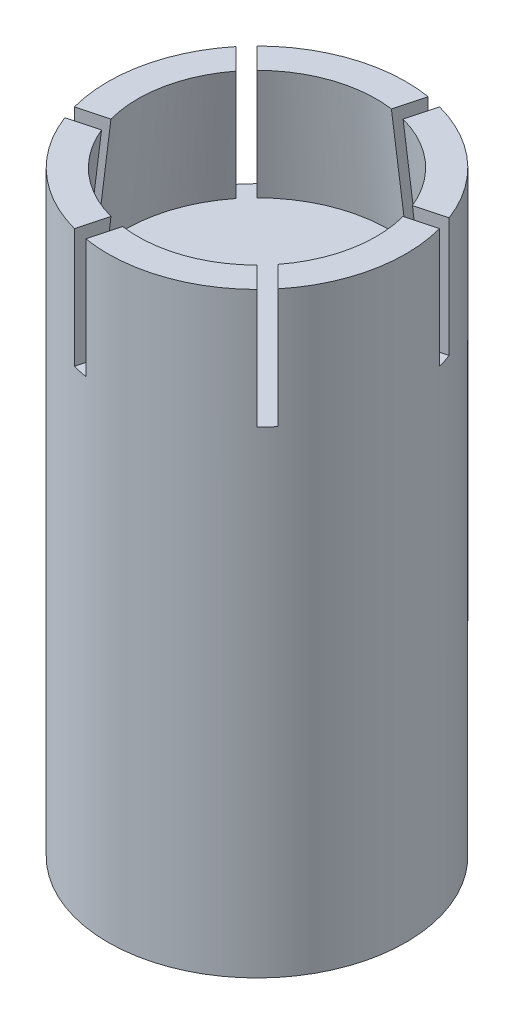
SolidWorks part; units mm, degrees
material "PE High Density"
ref_plane "Front Plane" through (0, 0, 0) normal (0, 0, 1) x (1, 0, 0)
ref_plane "Top Plane" through (0, 0, 0) normal (0, 1, 0) x (1, 0, 0)
ref_plane "Right Plane" through (0, 0, 0) normal (1, 0, 0) x (0, 0, -1)
sketch "Sketch2" plane through (0, 0, 0) normal (0, 0, 1) x (1, 0, 0)
  line L0 (0, 5.5338) -> (0, -28.1871) construction
  line L1 (0, -20) -> (5, -20)
  line L2 (5, -20) -> (5, 0)
  line L3 (5, 0) -> (0, 0)
  line L4 (0, 0) -> (0, -20) construction
  line L5 (0, 0) -> (0, -20)
  dimension "D1" = 20
  dimension "D5" = 5
revolve "Mount" add sketch "Sketch2" angle 360 about L0
sketch "Sketch3" plane through (0, 0, 0) normal (0, 1, 0) x (1, 0, 0)
  line L0 (-6.6225, 0) -> (9.9131, 0) construction
  line L1 (-4.2426, 4.2426) -> (0, 0)
  circle A0 centre (0, 0) radius 5 construction
  dimension "D2" = 6
  dimension "D1" = 45
extrude "Slots" cut sketch "Sketch3" against normal blind 4 and the other way blind 0.5 thin contours L1
pattern_circular "Slot CirPattern" count 6 over 360 about axis through (0, 0, 0) along (0, 1, 0) of "Slots"
sketch "Sketch4" plane through (0, 0, 0) normal (0, 1, 0) x (1, 0, 0)
  circle A1 centre (0, 0) radius 4
  arc A2 (0.6437, 3.9479) -> (-2.8284, 2.8284) centre (0, 0) ccw
  arc A3 (0.6437, 3.9479) -> (-2.8284, 2.8284) centre (0, 0) ccw construction
  dimension "D1" = 1
extrude "JoystickHole" cut sketch "Sketch4" against normal blind 4 draft 6 draft outward yes
